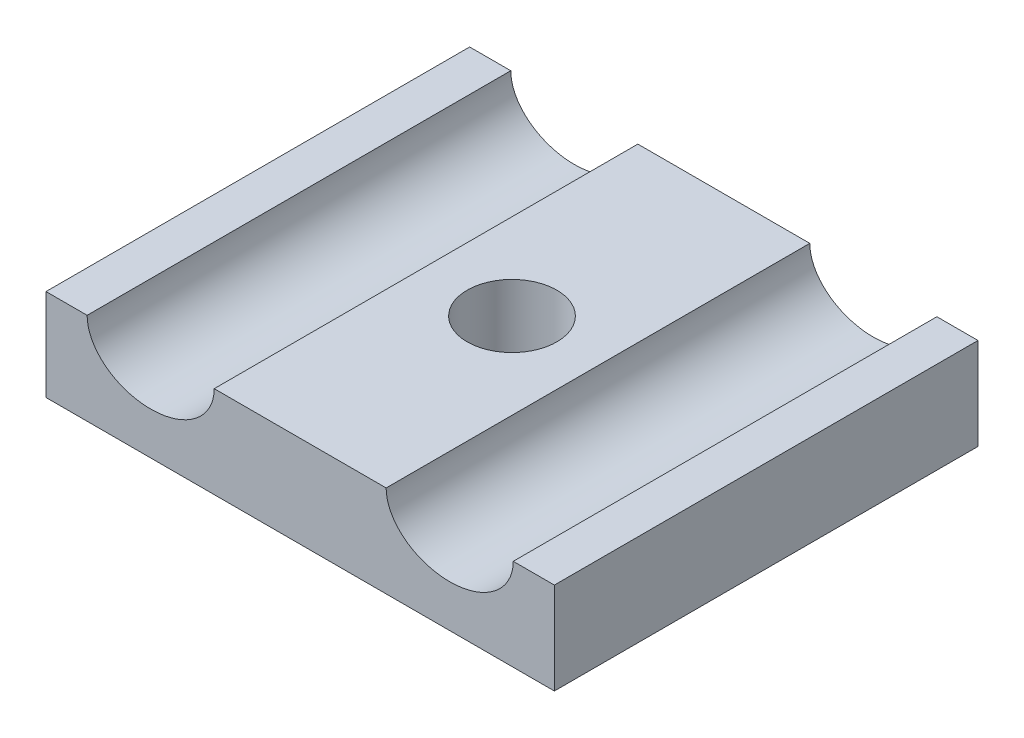
SolidWorks part; units mm, degrees
ref_plane "Front Plane" through (0, 0, 0) normal (0, 0, 1) x (1, 0, 0)
ref_plane "Top Plane" through (0, 0, 0) normal (0, 1, 0) x (1, 0, 0)
ref_plane "Right Plane" through (0, 0, 0) normal (1, 0, 0) x (0, 0, -1)
sketch "Sketch1" plane through (0, 0, 0) normal (0, 1, 0) x (1, 0, 0)
  line L1 (0, 0) -> (-36, 0)
  line L2 (0, 0) -> (0, -30)
  line L3 (0, -30) -> (-36, -30)
  line L4 (-36, 0) -> (-36, -30)
  dimension "D1" = 36
  dimension "D2" = 30
extrude "Boss-Extrude1" add sketch "Sketch1" along normal blind 6.5
sketch "Sketch2" plane through (0, 6.5, 0) normal (0, 1, 0) x (1, 0, 0)
  line L0 (-36, -30) -> (0, -30) construction
  circle A0 centre (-18, -15) radius 3.175
  point P4 (-18, -30)
extrude "Cut-Extrude1" cut sketch "Sketch2" against normal blind 5
sketch "Sketch3" plane through (0, 0, 30) normal (0, 0, 1) x (1, 0, 0)
  line L0 (-21.175, 6.5) -> (-36, 6.5) construction
  line L1 (-14.825, 6.5) -> (0, 6.5) construction
  line L2 (-18, 6.5) -> (-18, 0) construction
  line L3 (-36, 6.5) -> (0, 6.5) construction
  line L4 (-36, 0) -> (0, 0) construction
  line L5 (-18, 0) -> (-14.825, 0) construction
  line L6 (-14.825, 0) -> (-14.825, 6.5) construction
  line L7 (-21.175, 6.5) -> (-21.175, 0) construction
  line L8 (0, 6.5) -> (-36, 6.5) construction
  circle A1 centre (-7.4125, 6.5) radius 3.5
  circle A2 centre (-28.5875, 6.5) radius 3.5
  ellipse E0 centre (-7.4125, 6.5) end of major axis (-11.9125, 6.5) minor radius 3.5
  ellipse E1 centre (-28.5875, 6.5) end of major axis (-24.0875, 6.5) minor radius 3.5
  dimension "D1" = 3.175
  dimension "D3" = 4.5
  dimension "D4" = 7
  dimension "D2" = 3.175
  dimension "D5" = 3.5
  dimension "D6" = 9
extrude "Cut-Extrude3" cut sketch "Sketch3" against normal up to surface (30 mm away) contours E0 | E1 up to face at (-18, 3.25, 0)
